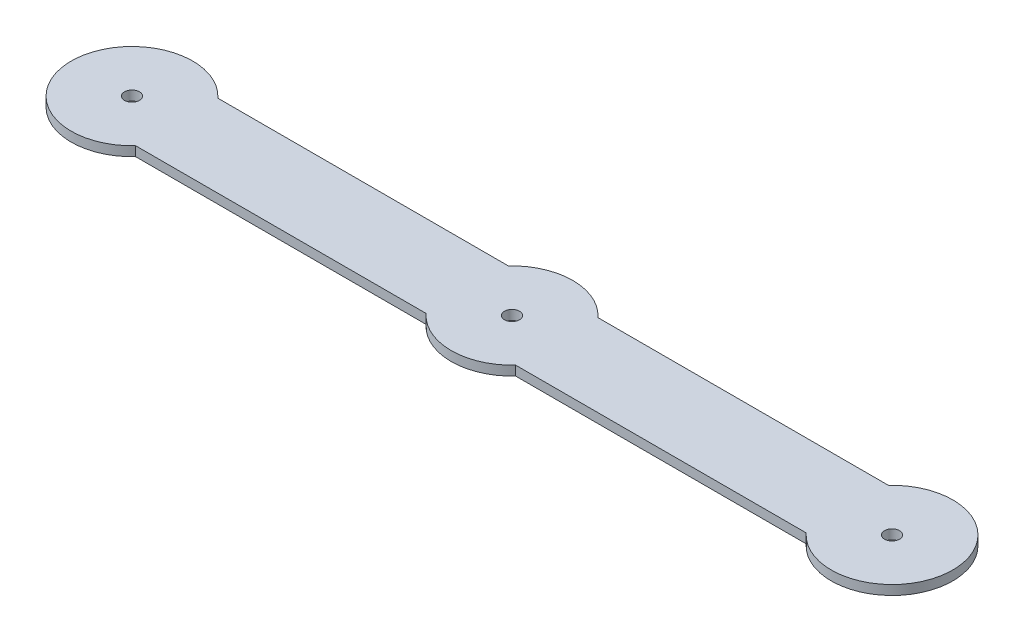
SolidWorks part; units mm, degrees
ref_plane "Front Plane" through (0, 0, 0) normal (0, 0, 1) x (1, 0, 0)
ref_plane "Top Plane" through (0, 0, 0) normal (0, 1, 0) x (1, 0, 0)
ref_plane "Right Plane" through (0, 0, 0) normal (1, 0, 0) x (0, 0, -1)
sketch "Sketch1" plane through (0, 0, 0) normal (0, 1, 0) x (1, 0, 0)
  line L0 (-89.636, 11) -> (-11.964, 11)
  line L1 (-89.636, -11) -> (-11.964, -11)
  line L2 (11.964, 11) -> (89.636, 11)
  line L3 (11.964, -11) -> (89.636, -11)
  arc A2 (-89.636, 11) -> (-89.636, -11) centre (-101.6, 0) ccw
  arc A3 (-11.964, -11) -> (11.964, -11) centre (0, 0) ccw
  arc A4 (89.636, -11) -> (89.636, 11) centre (101.6, 0) ccw
  arc A5 (11.964, 11) -> (-11.964, 11) centre (0, 0) ccw
  dimension "D5" = 32.5046
  dimension "D6" = 32.5046
  dimension "D7" = 32.5046
  dimension "D3" = 203.2
  dimension "D4" = 101.6
extrude "Boss-Extrude1" add sketch "Sketch1" along normal blind 2.54
sketch "Sketch2" plane through (0, 2.54, 0) normal (0, 1, 0) x (1, 0, 0)
  circle A0 centre (-101.6, 0) radius 2
  circle A1 centre (101.6, 0) radius 2
  circle A2 centre (0, 0) radius 2
  dimension "D2" = 4
  dimension "D4" = 4
  dimension "D5" = 4
  dimension "D1" = 101.6
  dimension "D3" = 101.6
extrude "Cut-Extrude1" cut sketch "Sketch2" against normal through all both and the other way through all
